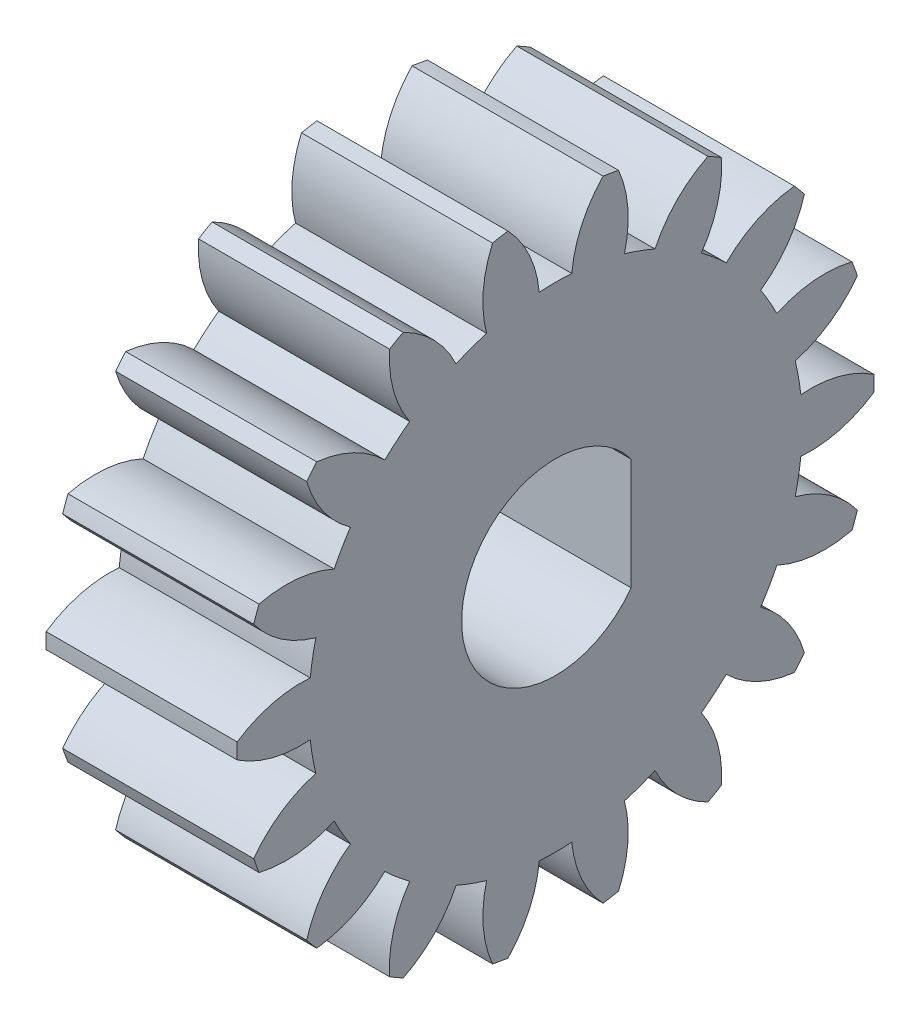
SolidWorks part; units mm, degrees
ref_plane "Plane1" through (0, 0, 0) normal (0, 0, 1) x (1, 0, 0)
ref_plane "Plane2" through (0, 0, 0) normal (0, 1, 0) x (1, 0, 0)
ref_plane "Plane3" through (0, 0, 0) normal (1, 0, 0) x (0, 0, -1)
sketch "HoldingSke" plane through (0, 0, 0) normal (0, 1, 0) x (1, 0, 0)
  line L0 (0, 0) -> (0.9511, -0.309)
  line L1 (-15, 0) -> (100, 0) construction
  line L2 (0, 0) -> (-2.1039, 2.3779)
  line L3 (0, 0) -> (-11.863, 4.5341)
  line L4 (0, 0) -> (8.2133, 2.6687)
  line L5 (0, 0) -> (-46.8476, -17.4728)
  line L6 (0, 0) -> (-4.9738, -3.3558)
  line L7 (-2.1039, 2.3779) -> (8.6588, 51.2066)
  line L8 (-76.2, 54.61) -> (-75.2, 54.61)
  line L9 (-71.009, 38.7566) -> (-53.1078, 45.2721)
  line L10 (-76.2, 71.12) -> (104.1128, 71.12)
  line L11 (0, 0) -> (-6, 0)
  line L12 (-76.2, 101.6) -> (-76.162, 101.6)
  line L13 (24.9733, 27.94) -> (52.9518, 28.4284)
  line L14 (24.9733, 27.94) -> (24.9743, 27.94)
  line L15 (24.9733, 27.94) -> (100.4006, 29.5858)
  line L16 (-63.627, -1) -> (-12.827, -1)
  circle A0 centre (0, 0) radius 3
  circle A1 centre (0, 0) radius 7.749
  circle A2 centre (0, 0) radius 37.5
  circle A3 centre (0, 0) radius 3
  dimension "MHD" = 15.498
  dimension "Hub_dia" = 75
  dimension "Bore" = 6
  dimension "MBD" = 6
  dimension "Num_teeth" = 18
  dimension "Pitch" = 1
  dimension "Overall_len" = 50
  dimension "Show_teeth" = 18
  dimension "Thickness" = 6
  dimension "OAL" = 50.0008
  dimension "T_dim" = 1
  dimension "Ap" = 20
  dimension "H" = 19.05
  dimension "Pitch_radius" = 180.3128
  dimension "Width" = 6
  dimension "Backlash" = 0.038
  dimension "Addendum_fac" = 1
  dimension "Dedendum_fac" = 1.25
  dimension "Clearance_fac" = 0.25
  dimension "Dedendum_add" = 0.001
  dimension "Module" = 1
sketch "BasProSke" plane through (0, 0, 0) normal (0, 1, 0) x (1, 0, 0)
  line L0 (-10, 0) -> (60, 0) construction
  line L1 (0, 0) -> (0, 10)
  line L2 (0, 0) -> (6, 0)
  line L3 (6, 0) -> (6, 10)
  line L4 (6, 10) -> (0, 10)
  dimension "Thickness" = 6
  dimension "Diameter" = 20
revolve "Base-Revolve" add sketch "BasProSke" angle 360 about L0
sketch "TooCutSke" plane through (0, 0, 0) normal (1, 0, 0) x (0, 0, -1)
  line L1 (0, 0) -> (0, 107) construction
  line L2 (0, 0) -> (-0.8509, 8.9597) construction
  line L3 (0, 0) -> (-3.1157, 17.6701) construction
  line L4 (-0.8509, 8.9597) -> (-1.5579, 8.835) construction
  arc A0 (0.5106, 7.7322) -> (-0.5106, 7.7322) centre (0, 0) ccw
  arc A1 (1.5152, 9.9102) -> (-1.5152, 9.9102) centre (0, 0) ccw
  circle A2 centre (0, 0) radius 9 construction
  circle A3 centre (0, 0) radius 8.4572 construction
  arc A4 (-0.5106, 7.7322) -> (-1.5152, 9.9102) centre (-4.0952, 7.3996) ccw
  arc A5 (1.5152, 9.9102) -> (0.5106, 7.7322) centre (4.0952, 7.3996) ccw
  dimension "Root_dia" = 15.498
  dimension "Overcut_dia" = 20.0508
  dimension "Pitch_dia" = 18
  dimension "Base_dia" = 16.9145
  dimension "Flank_rad" = 3.6
  dimension "Half_ang" = 10
  dimension "Half_CT" = 0.7179
extrude "ToothCut" cut sketch "TooCutSke" along normal through all
fillet "Breaks" [suppressed] radius 0.02
fillet "RootFillets" [suppressed] radius 0.251
pattern_circular "TeethCuts" count 18 every 20 about axis through (-10, 0, 0) along (1, 0, 0) of "ToothCut", "RootFillets", "Breaks"
sketch "HubNeaOneSke" plane through (0, 0, 0) normal (-1, 0, 0) x (0, 0, 1)
  circle A0 centre (0, 0) radius 7.749
  dimension "Diameter" = 15.498
extrude "HubNearOne" [suppressed] add sketch "HubNeaOneSke" along normal blind 44.0008
sketch "HubNeaBotSke" plane through (0, 0, 0) normal (-1, 0, 0) x (0, 0, 1)
  circle A0 centre (0, 0) radius 7.749
  dimension "Diameter" = 15.498
extrude "HubNearBoth" [suppressed] add sketch "HubNeaBotSke" along normal blind 22.0004
ref_plane "FarPln" through (6, 0, 0) normal (1, 0, 0) x (0, 0, -1)
sketch "HubFarSke" plane through (6, 0, 0) normal (1, 0, 0) x (0, 0, -1)
  circle A0 centre (0, 0) radius 7.749
  dimension "Diameter" = 15.498
extrude "HubFar" [suppressed] add sketch "HubFarSke" along normal blind 22.0004
sketch "KeySke" plane through (0, 0, 0) normal (1, 0, 0) x (0, 0, -1)
  line L0 (-1, 0) -> (-1, 4)
  line L1 (-1, 4) -> (1, 4)
  line L2 (1, 4) -> (1, 0)
  line L3 (0, 0) -> (0, 34) construction
  line L4 (-1, 0) -> (1, 0)
  dimension "Offset" = 4
  dimension "Width" = 2
extrude "Keyway" [suppressed] cut sketch "KeySke" along normal mid plane 100.0016
pattern_circular "Keyway2" [suppressed] count 2 every 90 about axis through (-10, 0, 0) along (1, 0, 0)
sketch "Sketch1" plane through (6, 0, 0) normal (1, 0, 0) x (0, 0, -1)
  line L0 (2.3749, 1.75) -> (2.3749, -1.75)
  arc A0 (2.3749, 1.75) -> (2.3749, -1.75) centre (0, 0) ccw
  dimension "D1" = 5.9
  dimension "D2" = 3.5
extrude "Cut-Extrude1" cut sketch "Sketch1" against normal through all
equation "' \"Module@HoldingSke\" = 6.35"
equation "' \"Num_teeth@HoldingSke\" = 12"
equation "' \"Ap@HoldingSke\" =  20"
equation "' \"Ap@HoldingSke\" = 20"
equation "' \"Width@HoldingSke\" = 0.5 * 25.4"
equation "' \"Hub_dia@HoldingSke\"= 1 * 25.4"
equation "' \"Hub_dia@HoldingSke\" = 1 * 25.4"
equation "' \"Overall_len@HoldingSke\" = 1.0 * 25.4"
equation "' \"T_dim@HoldingSke\" = 0.1 * 25.4"
equation "' \"Width@KeySke\" = 0.25 * 25.4"
equation "' \"Show_teeth@HoldingSke\" = 13"
equation "' \"Backlash@HoldingSke\" = 0.009 * 25.4"
equation "' \"Addendum_fac@HoldingSke\" = 1.0"
equation "' \"Dedendum_fac@HoldingSke\" = 1.25"
equation "' \"Dedendum_add@HoldingSke\" = 0.00005 * 25.4"
equation "' \"Clearance_fac@HoldingSke\" = 0.25"
equation "\"Pitch@HoldingSke\" = 1 / \"Module@HoldingSke\""
equation "\"Overcut_dia@TooCutSke\" = (\"Num_teeth@HoldingSke\" + 2 * \"Addendum_fac@HoldingSke\") / \"Pitch@HoldingSke\" + 0.002 * 25.4"
equation "\"Pitch_dia@TooCutSke\" = \"Num_teeth@HoldingSke\" / \"Pitch@HoldingSke\""
equation "\"Base_dia@TooCutSke\" = \"Num_teeth@HoldingSke\" / \"Pitch@HoldingSke\" * cos((\"Ap@HoldingSke\"  * 3.14159265 / 180))"
equation "\"Root_dia@TooCutSke\" = (\"Num_teeth@HoldingSke\" + 2) / \"Pitch@HoldingSke\" - 2 * (\"Addendum_fac@HoldingSke\" + \"Dedendum_fac@HoldingSke\") / \"Pitch@HoldingSke\" - \"Dedendum_add@HoldingSke\" * 2"
equation "\"Half_ang@TooCutSke\" = 180 / \"Num_teeth@HoldingSke\""
equation "\"Half_CT@TooCutSke\" = \"Num_teeth@HoldingSke\" / \"Pitch@HoldingSke\" * sin((3.14159265 / 2 / \"Num_teeth@HoldingSke\")) / 2 - 7 * \"Backlash@HoldingSke\" / 4"
equation "\"Flank_rad@TooCutSke\" = \"Num_teeth@HoldingSke\" / \"Pitch@HoldingSke\" / 5"
equation "\"Radius@RootFillets\" = \"Clearance_fac@HoldingSke\" / \"Pitch@HoldingSke\" + \"Dedendum_add@HoldingSke\""
equation "\"Break_rad@Breaks\" = 0.02 / \"Pitch@HoldingSke\""
equation "\"Thickness@HoldingSke\" = \"Width@HoldingSke\""
equation "\"OAL@HoldingSke\" = \"Thickness@HoldingSke\""
equation "\"MHD@HoldingSke\" = (\"Num_teeth@HoldingSke\" + 2) / \"Pitch@HoldingSke\" - 2 * (\"Addendum_fac@HoldingSke\" + \"Dedendum_fac@HoldingSke\")  / \"Pitch@HoldingSke\" - \"Dedendum_add@HoldingSke\" * 2"
equation "\"MBD@HoldingSke\" = (\"Num_teeth@HoldingSke\" + 2) / \"Pitch@HoldingSke\" - 2 * (\"Addendum_fac@HoldingSke\" + \"Dedendum_fac@HoldingSke\")  / \"Pitch@HoldingSke\" - \"Dedendum_add@HoldingSke\" * 2 - 0.002 * 25.4"
equation "\"MHD@HoldingSke\" = ((sgn( \"MHD@HoldingSke\" - \"Hub_dia@HoldingSke\" )-1)*( \"MHD@HoldingSke\" - \"Hub_dia@HoldingSke\" ))/-2+ \"Hub_dia@HoldingSke\""
equation "\"MBD@HoldingSke\" = ((sgn( \"MBD@HoldingSke\" - \"Bore@HoldingSke\" )-1)*( \"MBD@HoldingSke\" - \"Bore@HoldingSke\" ))/-2+ \"Bore@HoldingSke\""
equation "\"OAL@HoldingSke\" = ((sgn( \"OAL@HoldingSke\" - \"Overall_len@HoldingSke\" )+1)*( \"OAL@HoldingSke\" - \"Overall_len@HoldingSke\" ))/2 + \"Overall_len@HoldingSke\" + 0.000002 * 25.4"
equation "\"Num_teeth@TeethCuts\" = int( \"Show_teeth@HoldingSke\" ) + 1"
equation "\"Num_teeth@TeethCuts\" = ((sgn( \"Num_teeth@TeethCuts\" - \"Num_teeth@HoldingSke\" )-1)*( \"Num_teeth@TeethCuts\" - \"Num_teeth@HoldingSke\" ))/-2+ \"Num_teeth@HoldingSke\""
equation "\"Num_teeth@TeethCuts\" = ((sgn( \"Num_teeth@TeethCuts\" - 2.0)+1)*( \"Num_teeth@TeethCuts\" - 2.0))/2 +2.0"
equation "\"Angle@TeethCuts\" = 360.0 / \"Num_teeth@HoldingSke\""
equation "\"Diameter@BasProSke\" = (\"Num_teeth@HoldingSke\" + 2 * \"Addendum_fac@HoldingSke\") / \"Pitch@HoldingSke\""
equation "\"Thickness@BasProSke\"  = \"Thickness@HoldingSke\""
equation "' \"Fillet_rad@BasProSke\" =  \"Thickness@HoldingSke\" * 0.05"
equation "' \"Fillet_rad@BasProSke\" = \"Thickness@HoldingSke\" * 0.05"
equation "\"MHD@HoldingSke\" = ((sgn( \"MHD@HoldingSke\" - \"Root_dia@TooCutSke\" )-1)*( \"MHD@HoldingSke\" - \"Root_dia@TooCutSke\" ))/-2+ \"Root_dia@TooCutSke\""
equation "\"Diameter@HubNeaOneSke\" = \"MHD@HoldingSke\""
equation "\"Length@HubNearOne\" = \"OAL@HoldingSke\" - \"Thickness@BasProSke\""
equation "\"Diameter@HubNeaBotSke\" = \"MHD@HoldingSke\""
equation "\"Length@HubNearBoth\" = ( \"OAL@HoldingSke\" - \"Thickness@BasProSke\" ) / 2.0"
equation "\"Thickness@FarPln\" = \"Thickness@BasProSke\""
equation "\"Diameter@HubFarSke\" = \"MHD@HoldingSke\""
equation "\"Length@HubFar\" = ( \"OAL@HoldingSke\" - \"Thickness@BasProSke\" ) / 2.0"
equation "\"D1@Keyway\" = \"OAL@HoldingSke\" * 2.0"
equation "\"Offset@KeySke\" = \"T_dim@HoldingSke\" + \"MBD@HoldingSke\" / 2.0"
